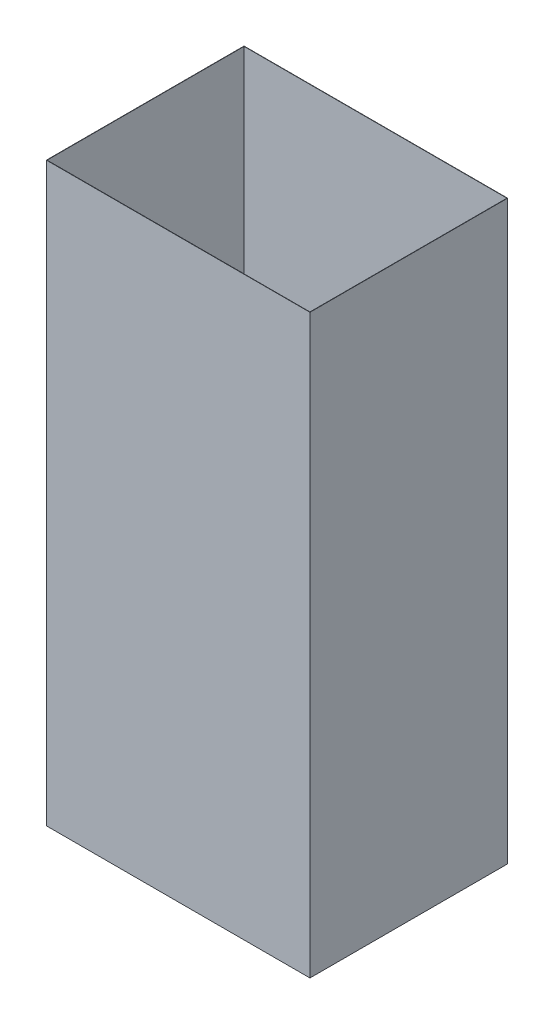
SolidWorks part; units mm, degrees
ref_plane "Front Plane" through (0, 0, 0) normal (0, 0, 1) x (1, 0, 0)
ref_plane "Top Plane" through (0, 0, 0) normal (0, 1, 0) x (1, 0, 0)
ref_plane "Right Plane" through (0, 0, 0) normal (1, 0, 0) x (0, 0, -1)
sketch "Sketch1" plane through (0, 0, 0) normal (0, 1, 0) x (1, 0, 0)
  line L1 (-203.2, 152.4) -> (203.2, 152.4)
  line L2 (-203.2, 152.4) -> (-203.2, -152.4)
  line L3 (-203.2, -152.4) -> (203.2, -152.4)
  line L4 (203.2, 152.4) -> (203.2, -152.4)
  line L5 (-203.2, 152.4) -> (203.2, -152.4) construction
  line L6 (-203.2, -152.4) -> (203.2, 152.4) construction
  point P0 (0, 0)
  dimension "D1" = 406.4
  dimension "D2" = 304.8
extrude "Boss-Extrude1" add sketch "Sketch1" along normal blind 889
shell "Shell1" thickness 0.508
